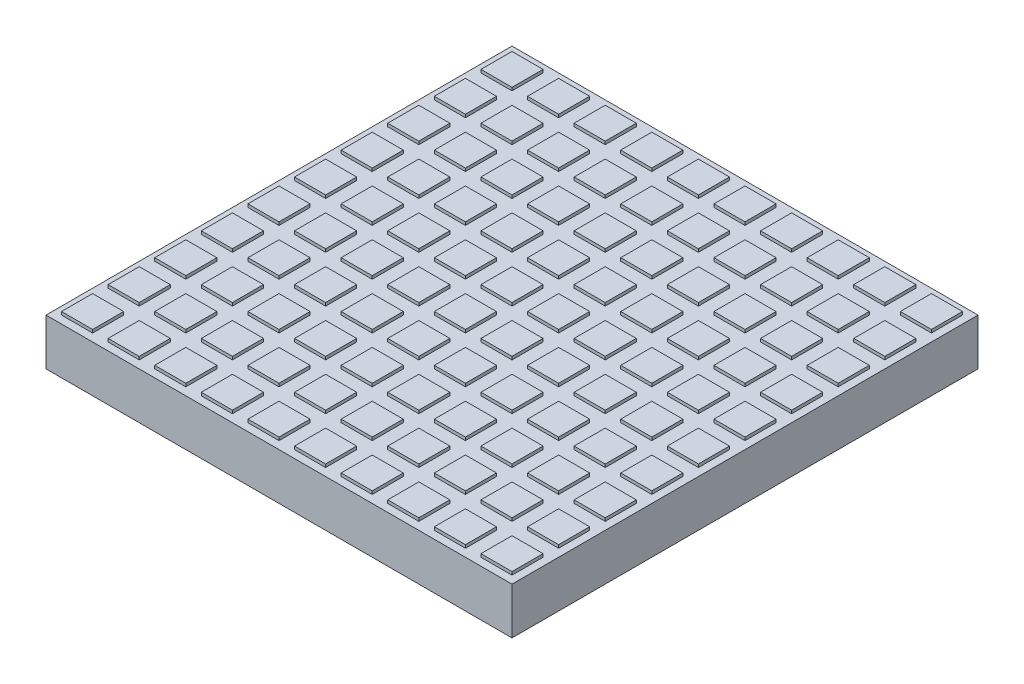
SolidWorks part; units mm, degrees
ref_plane "Front Plane" through (0, 0, 0) normal (0, 0, 1) x (1, 0, 0)
ref_plane "Top Plane" through (0, 0, 0) normal (0, 1, 0) x (1, 0, 0)
ref_plane "Right Plane" through (0, 0, 0) normal (1, 0, 0) x (0, 0, -1)
sketch "Sketch1" plane through (0, 0, 0) normal (0, 1, 0) x (1, 0, 0)
  line L1 (0, 0) -> (300, 0)
  line L2 (0, 0) -> (0, 300)
  line L3 (0, 300) -> (300, 300)
  line L4 (300, 0) -> (300, 300)
  dimension "D1" = 300
  dimension "D2" = 300
extrude "Boss-Extrude1" add sketch "Sketch1" along normal blind 30
sketch "Sketch2" plane through (0, 30, 0) normal (0, 1, 0) x (1, 0, 0)
  line L0 (0, 300) -> (0, 0) construction
  line L1 (5, 295) -> (25, 295)
  line L2 (5, 295) -> (5, 275)
  line L3 (5, 275) -> (25, 275)
  line L4 (25, 295) -> (25, 275)
  line L5 (300, 300) -> (0, 300) construction
  dimension "D1" = 20
  dimension "D2" = 20
  dimension "D3" = 5
  dimension "D4" = 5
extrude "Boss-Extrude2" add sketch "Sketch2" along normal blind 2
pattern_linear "LPattern1" count 10 spacing 30 along (1, 0, 0) count 10 spacing 30 along (0, 0, 1) of "Boss-Extrude2"
